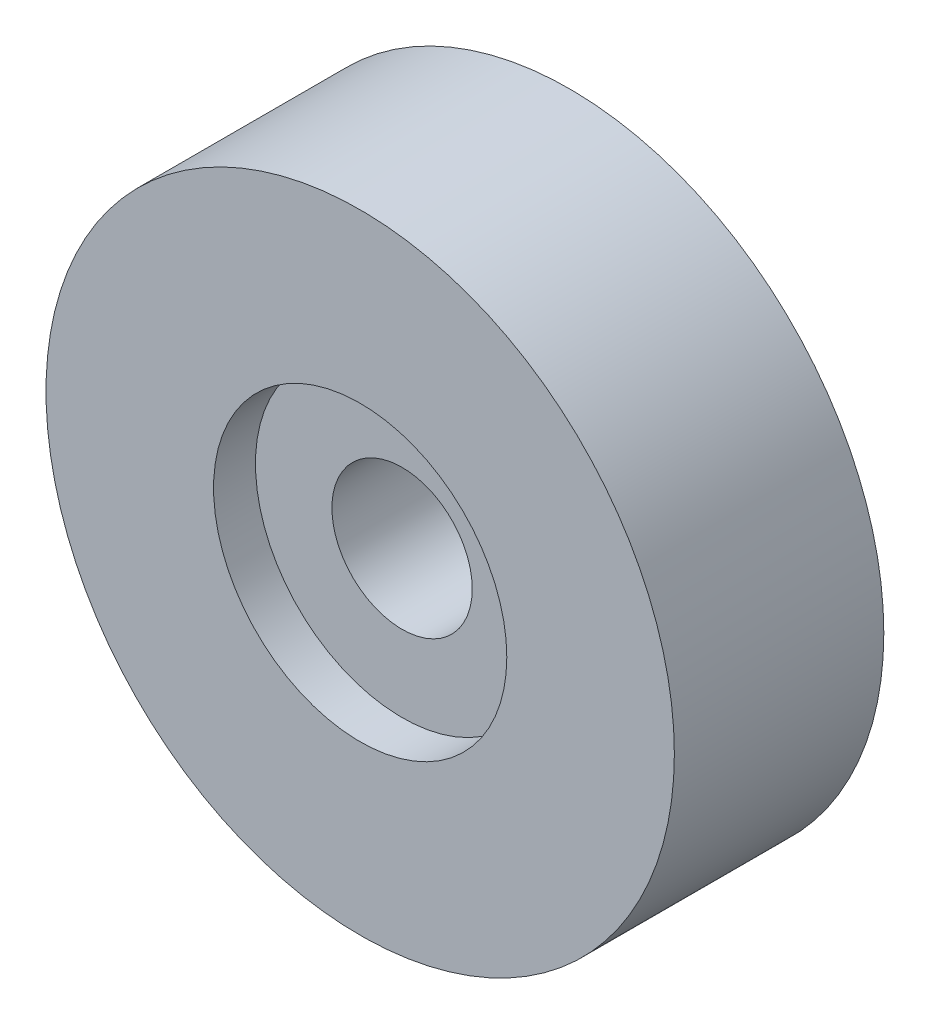
SolidWorks part; units mm, degrees
material "ABS PC"
ref_plane "Ebene vorne" through (0, 0, 0) normal (0, 0, 1) x (1, 0, 0)
ref_plane "Ebene oben" through (0, 0, 0) normal (0, 1, 0) x (1, 0, 0)
ref_plane "Ebene rechts" through (0, 0, 0) normal (1, 0, 0) x (0, 0, -1)
sketch "Skizze1" plane through (0, 0, 0) normal (0, 0, 1) x (1, 0, 0)
  circle A0 centre (0, 0) radius 15
  circle A1 centre (0, 0) radius 3.35
  dimension "D1" = 30
  dimension "D2" = 6.7
extrude "Aufsatz-Linear austragen1" add sketch "Skizze1" along normal blind 10
sketch "Skizze2" plane through (0, 0, 10) normal (0, 0, 1) x (1, 0, 0)
  circle A0 centre (0, 0) radius 7
  dimension "D1" = 14
extrude "Schnitt-Linear austragen1" cut sketch "Skizze2" against normal blind 2
